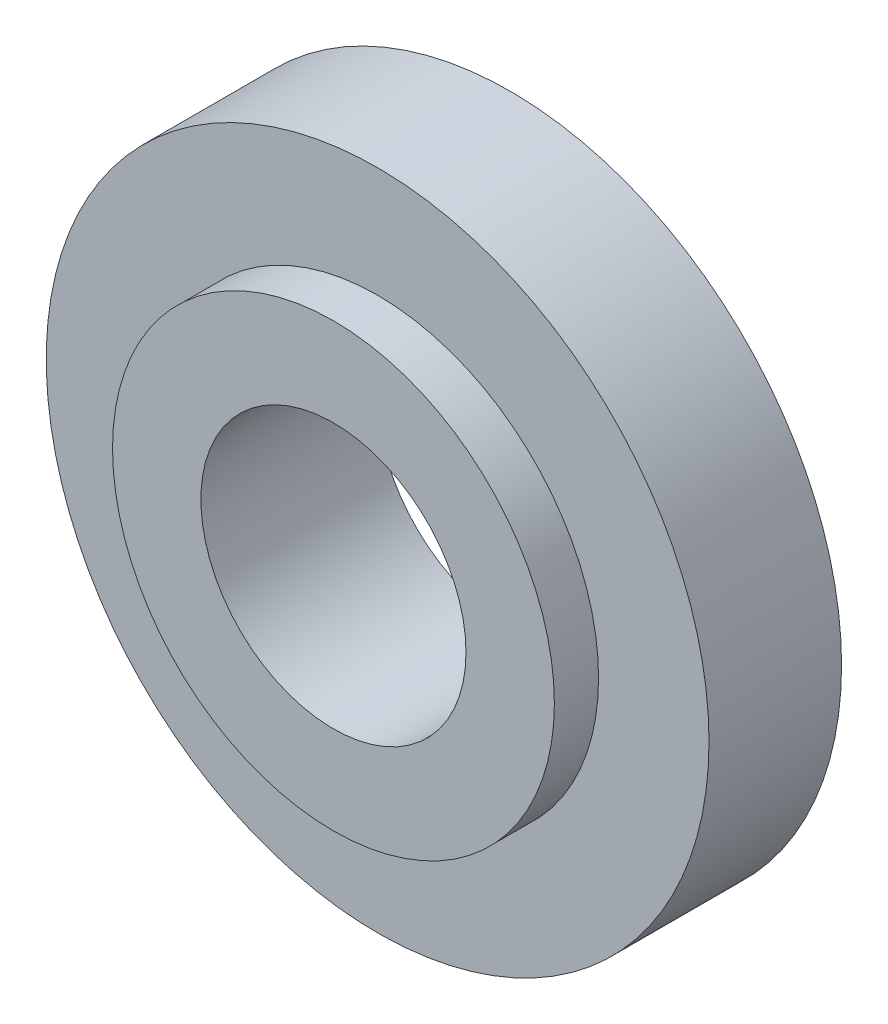
SolidWorks part; units mm, degrees
ref_plane "Front Plane" through (0, 0, 0) normal (0, 0, 1) x (1, 0, 0)
ref_plane "Top Plane" through (0, 0, 0) normal (0, 1, 0) x (1, 0, 0)
ref_plane "Right Plane" through (0, 0, 0) normal (1, 0, 0) x (0, 0, -1)
sketch "Sketch1" plane through (0, 0, 0) normal (0, 0, 1) x (1, 0, 0)
  circle A0 centre (0, 0) radius 3.75
  dimension "D1" = 7.5
extrude "Boss-Extrude2" add sketch "Sketch1" along normal blind 1.5 contours A0
sketch "Sketch2" plane through (0, 0, 1.5) normal (0, 0, 1) x (1, 0, 0)
  circle A0 centre (0, 0) radius 2.5
  dimension "D1" = 5
extrude "Boss-Extrude3" add sketch "Sketch2" along normal blind 0.5
sketch "Sketch3" plane through (0, 0, 2) normal (0, 0, 1) x (1, 0, 0)
  circle A0 centre (0, 0) radius 1.5
  dimension "D1" = 3
extrude "Cut-Extrude2" cut sketch "Sketch3" against normal through all both and the other way through all
